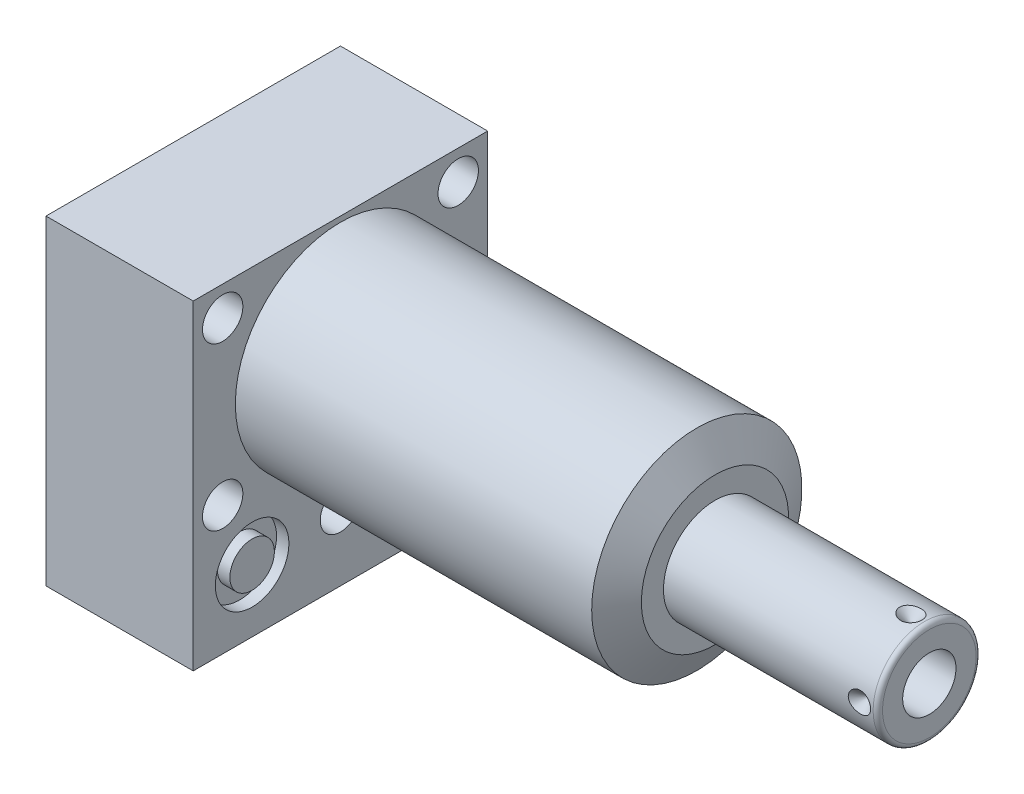
SolidWorks part; units mm, degrees
material "Alloy Steel"
ref_plane "Front Plane" through (0, 0, 0) normal (0, 0, 1) x (1, 0, 0)
ref_plane "Top Plane" through (0, 0, 0) normal (0, 1, 0) x (1, 0, 0)
ref_plane "Right Plane" through (0, 0, 0) normal (1, 0, 0) x (0, 0, -1)
ref_plane "Plane1" through (0, 0, 0) normal (1, 0, 0) x (0, 0, -1)
sketch "Sketch1" plane through (0, 0, 0) normal (1, 0, 0) x (0, 0, -1)
  line L0 (-31.75, 23.8252) -> (-31.75, -45.2628)
  line L1 (-31.75, -45.2628) -> (31.75, -45.2628)
  line L2 (31.75, -45.2628) -> (31.75, 23.8252)
  line L3 (31.75, 23.8252) -> (-31.75, 23.8252)
  line L4 (0, -55.6514) -> (0, 27.6098) construction
  dimension "D1" = 63.5
  dimension "D2" = 69.088
  dimension "D3" = 23.8252
extrude "Extrude1" add sketch "Sketch1" along normal blind 80.772 and the other way blind 31.75
ref_plane "Plane2" through (0, 0, 0) normal (1, 0, 0) x (0, 0, -1)
sketch "Sketch2" plane through (0, 0, 0) normal (1, 0, 0) x (0, 0, -1)
  line L0 (-26.0541, 0) -> (26.0541, 0) construction
  line L5 (31.75, 23.8252) -> (-31.75, 23.8252)
  line L6 (-31.75, 23.8252) -> (-31.75, -45.2628)
  line L7 (-31.75, -45.2628) -> (31.75, -45.2628)
  line L8 (31.75, -45.2628) -> (31.75, 23.8252)
  line L9 (31.75, 23.8252) -> (-31.75, 23.8252)
  line L10 (-31.75, 23.8252) -> (-31.75, -45.2628)
  line L11 (-31.75, -45.2628) -> (31.75, -45.2628)
  line L12 (31.75, -45.2628) -> (31.75, 23.8252)
  circle A0 centre (0, 0) radius 22.6695
  dimension "D1" = 45.339
  dimension "D2" = 0
extrude "Cut-Extrude1" cut sketch "Sketch2" along normal up to next
ref_plane "Plane3" through (0, 0, 0) normal (0, 0, 1) x (1, 0, 0)
sketch "Sketch3" plane through (0, 0, 0) normal (0, 0, 1) x (1, 0, 0)
  line L0 (76.8492, 22.6695) -> (80.772, 15.875)
  line L1 (76.0371, 0) -> (80.9975, 0) construction
  line L2 (80.772, 22.6695) -> (80.772, 15.875)
  line L3 (80.772, 22.6695) -> (76.8492, 22.6695)
  line L4 (80.772, 22.6695) -> (0, 22.6695) construction
  line L5 (80.772, -22.6695) -> (80.772, 22.6695) construction
  dimension "D1" = 31.75
  dimension "D2" = 30
revolve "Cut-Revolve1" cut sketch "Sketch3" angle 360 about L1
ref_plane "Plane4" through (-29.083, -31.75, 19.05) normal (0, 0, 1) x (0, 1, 0)
sketch "S2D0002" plane through (-29.083, -31.75, 19.05) normal (0, 0, 1) x (0, 1, 0)
  line L0 (0, 0) -> (4.5466, 0)
  line L1 (4.5466, 0) -> (4.1066, -2.0701)
  line L2 (4.1066, -2.0701) -> (3.4544, -2.7223)
  line L3 (3.4544, -2.7223) -> (3.4544, -13.97)
  line L4 (3.4544, -13.97) -> (0, -13.97)
  line L5 (0, -13.97) -> (0, 0)
  line L6 (0, -14.6685) -> (0, 0.6985) construction
  dimension "D1" = 13.97
revolve "Cut-Revolve2" cut sketch "S2D0002" angle 360 about L6
ref_plane "Plane5" through (-29.083, -31.75, -19.05) normal (0, 0, 1) x (0, 1, 0)
sketch "Sketch5" plane through (-29.083, -31.75, -19.05) normal (0, 0, 1) x (0, 1, 0)
  line L0 (0, 0) -> (4.5466, 0)
  line L1 (4.5466, 0) -> (4.1066, -2.0701)
  line L2 (4.1066, -2.0701) -> (3.4544, -2.7223)
  line L3 (3.4544, -2.7223) -> (3.4544, -13.97)
  line L4 (3.4544, -13.97) -> (0, -13.97)
  line L5 (0, -13.97) -> (0, 0)
  line L6 (0, -14.6685) -> (0, 0.6985) construction
  dimension "D1" = 13.97
revolve "Cut-Revolve3" cut sketch "Sketch5" angle 360 about L6
ref_plane "Plane6" through (-2.667, -31.75, 19.05) normal (0, 0, 1) x (0, -1, 0)
sketch "Sketch6" plane through (-2.667, -31.75, 19.05) normal (0, 0, 1) x (0, -1, 0)
  line L0 (0, 0) -> (4.5466, 0)
  line L1 (4.5466, 0) -> (4.1066, -2.0701)
  line L2 (4.1066, -2.0701) -> (3.4544, -2.7223)
  line L3 (3.4544, -2.7223) -> (3.4544, -12.192)
  line L4 (3.4544, -12.192) -> (0, -12.192)
  line L5 (0, -12.192) -> (0, 0)
  line L6 (0, -12.8016) -> (0, 0.6096) construction
  dimension "D1" = 12.192
revolve "Cut-Revolve4" cut sketch "Sketch6" angle 360 about L6
ref_plane "Plane7" through (-2.667, -31.75, -19.05) normal (0, 0, 1) x (0, -1, 0)
sketch "Sketch7" plane through (-2.667, -31.75, -19.05) normal (0, 0, 1) x (0, -1, 0)
  line L0 (0, 0) -> (4.5466, 0)
  line L1 (4.5466, 0) -> (4.1066, -2.0701)
  line L2 (4.1066, -2.0701) -> (3.4544, -2.7223)
  line L3 (3.4544, -2.7223) -> (3.4544, -12.192)
  line L4 (3.4544, -12.192) -> (0, -12.192)
  line L5 (0, -12.192) -> (0, 0)
  line L6 (0, -12.8016) -> (0, 0.6096) construction
  dimension "D1" = 12.192
revolve "Cut-Revolve5" cut sketch "Sketch7" angle 360 about L6
ref_plane "Plane8" through (-15.875, -51.6128, 19.05) normal (0, 0, 1) x (-1, 0, 0)
sketch "Sketch8" plane through (-15.875, -51.6128, 19.05) normal (0, 0, 1) x (-1, 0, 0)
  line L0 (0, -6.604) -> (6.1849, -6.604)
  line L1 (6.1849, -6.604) -> (5.6423, -9.1567)
  line L2 (5.6423, -9.1567) -> (4.9784, -9.8206)
  line L3 (4.9784, -9.8206) -> (4.9784, -25.654)
  line L4 (4.9784, -25.654) -> (0, -25.654)
  line L5 (0, -25.654) -> (0, -6.604)
  line L6 (0, -26.67) -> (0, 1.27) construction
  line L7 (15.875, -6.35) -> (-15.875, -6.35) construction
  dimension "D1" = 19.05
  dimension "D2" = 0.254
revolve "Cut-Revolve6" cut sketch "Sketch8" angle 360 about L6
ref_plane "Plane9" through (-15.875, -51.6128, -19.05) normal (0, 0, 1) x (-1, 0, 0)
sketch "Sketch9" plane through (-15.875, -51.6128, -19.05) normal (0, 0, 1) x (-1, 0, 0)
  line L0 (0, -6.604) -> (6.1849, -6.604)
  line L1 (6.1849, -6.604) -> (5.6423, -9.1567)
  line L2 (5.6423, -9.1567) -> (4.9784, -9.8206)
  line L3 (4.9784, -9.8206) -> (4.9784, -25.654)
  line L4 (4.9784, -25.654) -> (0, -25.654)
  line L5 (0, -25.654) -> (0, -6.604)
  line L6 (0, -26.67) -> (0, 1.27) construction
  line L7 (15.875, -6.35) -> (-15.875, -6.35) construction
  dimension "D1" = 19.05
  dimension "D2" = 0.254
revolve "Cut-Revolve7" cut sketch "Sketch9" angle 360 about L6
ref_plane "Plane10" through (0, 0, 0) normal (0, 0, 1) x (1, 0, 0)
sketch "Sketch18" plane through (0, 0, 0) normal (1, 0, 0) x (0, 0, -1)
  circle A0 centre (-19.05, -31.75) radius 7.9375
  circle A1 centre (19.05, -31.75) radius 7.9375
  dimension "D1" = 15.875
extrude "Cut-Extrude2" cut sketch "Sketch18" against normal blind 2.667
sketch "Sketch19" plane through (-31.75, 0, 0) normal (-1, 0, 0) x (0, 0, 1)
  circle A0 centre (-19.05, -31.75) radius 7.9375
  circle A1 centre (19.05, -31.75) radius 7.9375
  dimension "D1" = 15.875
extrude "Cut-Extrude3" cut sketch "Sketch19" against normal blind 2.667
sketch "Sketch20" plane through (0, -45.2628, 0) normal (0, -1, 0) x (1, 0, 0)
  circle A0 centre (-15.875, -19.05) radius 9.525
  circle A1 centre (-15.875, 19.05) radius 9.525
  circle A2 centre (-15.875, 19.05) radius 6.1849 construction
  dimension "D1" = 19.05
extrude "Cut-Extrude4" cut sketch "Sketch20" against normal blind 0.254
sketch "Sketch10" plane through (0, 0, 0) normal (0, 0, 1) x (1, 0, 0)
  line L0 (80.772, 0) -> (80.772, 11.1125)
  line L1 (80.772, 11.1125) -> (125.984, 11.1125)
  line L2 (127, 10.0965) -> (127, 0)
  line L3 (127, 0) -> (80.772, 0)
  line L4 (58.2708, 0) -> (120.537, 0) construction
  line L5 (80.772, -15.875) -> (80.772, 15.875) construction
  line L6 (-31.75, 23.8252) -> (-31.75, -45.2628) construction
  arc A0 (127, 10.0965) -> (125.984, 11.1125) centre (125.984, 10.0965) ccw
  point P0 (80.772, 0)
  dimension "D2" = 1.016
  dimension "D1" = 22.225
  dimension "D3" = 158.75
revolve "Revolve1" add sketch "Sketch10" angle 360 about L4
ref_plane "Plane11" through (118.6434, -5.7531, 0) normal (0, 0, 1) x (0, -1, 0)
sketch "S2D0001" plane through (118.6434, -5.7531, 0) normal (0, 0, 1) x (0, -1, 0)
  line L0 (0, 8.3566) -> (0, -8.6614)
  line L1 (0, -8.6614) -> (-5.7531, -12.1182)
  line L2 (0, 8.3566) -> (-5.7531, 8.3566)
  line L3 (-5.7531, 8.3566) -> (-5.7531, -12.1182)
  line L4 (-5.7531, -34.3471) -> (-5.7531, 1.0237) construction
  line L5 (4.3434, 8.3566) -> (-15.8496, 8.3566) construction
  dimension "D1" = 11.5062
  dimension "D2" = 17.018
  dimension "D3" = 59
revolve "Cut-Revolve8" cut sketch "S2D0001" angle 360 about L4
ref_plane "Plane12" through (-31.75, -51.6128, 0) normal (0, -1, 0) x (0, 0, -1)
sketch "Sketch12" plane through (-31.75, -45.0088, 0) normal (0, -1, 0) x (0, 0, -1)
  circle A0 centre (-19.05, 15.875) radius 6.4389
  circle A1 centre (-19.05, 15.875) radius 9.525 construction
  dimension "D1" = 12.8778
extrude "Extrude2" add sketch "Sketch12" along normal blind 1.651
sketch "Sketch13" plane through (0, 0, 0) normal (1, 0, 0) x (0, 0, -1)
  circle A0 centre (-19.05, -31.75) radius 4.8006
  circle A1 centre (-19.05, -31.75) radius 7.9375 construction
  dimension "D1" = 9.6012
ref_plane "Plane13" through (-31.75, 0, 0) normal (1, 0, 0) x (0, 0, -1)
extrude "Extrude3" add sketch "Sketch13" along normal up to surface
ref_plane "Plane14" through (0, -31.75, -19.05) normal (0, -1, 0) x (0, 0, -1)
sketch "Sketch14" plane through (0, -31.75, -19.05) normal (0, -1, 0) x (0, 0, -1)
  line L0 (0, -2.8435) -> (0, 1.0401) construction
  line L1 (0, -5.3893) -> (0, -12.2901) construction
  line L2 (7.9375, -2.667) -> (-7.9375, -2.667) construction
  circle A0 centre (6.1722, -0.9017) radius 1.7653
  dimension "D1" = 3.5306
  dimension "D2" = 12.3444
revolve "Revolve2" add sketch "Sketch14" angle 360 about L0
ref_plane "Plane15" through (0, -31.75, -19.05) normal (0, -1, 0) x (0, 0, -1)
sketch "Sketch15" plane through (0, -31.75, -19.05) normal (0, -1, 0) x (0, 0, -1)
  line L0 (0, -32.7901) -> (0, -28.9065) construction
  line L1 (0, -29.083) -> (0, -27.0129) construction
  line L2 (-7.9375, -29.083) -> (7.9375, -29.083) construction
  circle A0 centre (6.1722, -30.8483) radius 1.7653
  dimension "D1" = 3.5306
  dimension "D2" = 12.3444
revolve "Revolve3" add sketch "Sketch15" angle 360 about L0
ref_plane "Plane18" through (0, 0, 0) normal (0, 0.7071, 0.7071) x (-1, 0, 0)
ref_plane "Plane16" through (114.681, -11.1125, 0) normal (0, 0, 1) x (-1, 0, 0)
sketch "Sketch16" plane through (114.681, 11.1125, 0) normal (0, 0, -1) x (-1, 0, 0)
  line L0 (-8.3566, 0) -> (-5.9436, 0)
  line L1 (-5.9436, 0) -> (-8.3566, -2.413)
  line L2 (-8.3566, 0) -> (-8.3566, -2.413)
  line L3 (-8.3566, -5.0193) -> (-8.3566, 0.1207) construction
  line L4 (33.909, 0) -> (-11.303, 0) construction
  line L5 (-12.319, -1.016) -> (-12.319, -21.209) construction
  dimension "D1" = 3.9624
  dimension "D2" = 4.826
  dimension "D3" = 45
ref_plane "Plane17" through (114.681, 11.1125, 0) normal (0, 0, 1) x (1, 0, 0)
revolve "Cut-Revolve9" cut sketch "Sketch16" angle 360 about L3
hole_wizard "Hole1" positions "Sketch22" profile "Sketch21" legacy end condition up to next
sketch "Sketch22" plane through (0, 0, 0) normal (1, 0, 0) x (0, 0, -1)
  line L0 (0, 0) -> (-38.8053, 0) construction
  line L1 (0, 0) -> (0, 31.2017) construction
  point P0 (-25.4, 17.4752)
  point P1 (0, -30.8356)
  point P12 (-25.4, -17.4752)
  point P14 (25.4, 17.4752)
  point P15 (25.4, -17.4752)
  dimension "D1" = 25.4
  dimension "D2" = 17.4752
  dimension "D3" = 30.8356
sketch "Sketch21" plane through (0, 17.4752, 25.4) normal (0, 1, 0) x (0, 0, -1)
  line L0 (0, 0) -> (0, 31.75)
  line L1 (0, 31.75) -> (4.3561, 31.75)
  line L2 (4.3561, 31.75) -> (4.3561, 0)
  line L3 (4.3561, 0) -> (0, 0)
  line L4 (0, 110) -> (0, -10) construction
  dimension "Diameter" = 8.7122
  dimension "Depth" = 31.75
pattern_circular "CirPattern1" count 4 over 360 about axis through (58.2708, 0, 0) along (-1, 0, 0) of "Cut-Revolve9"
